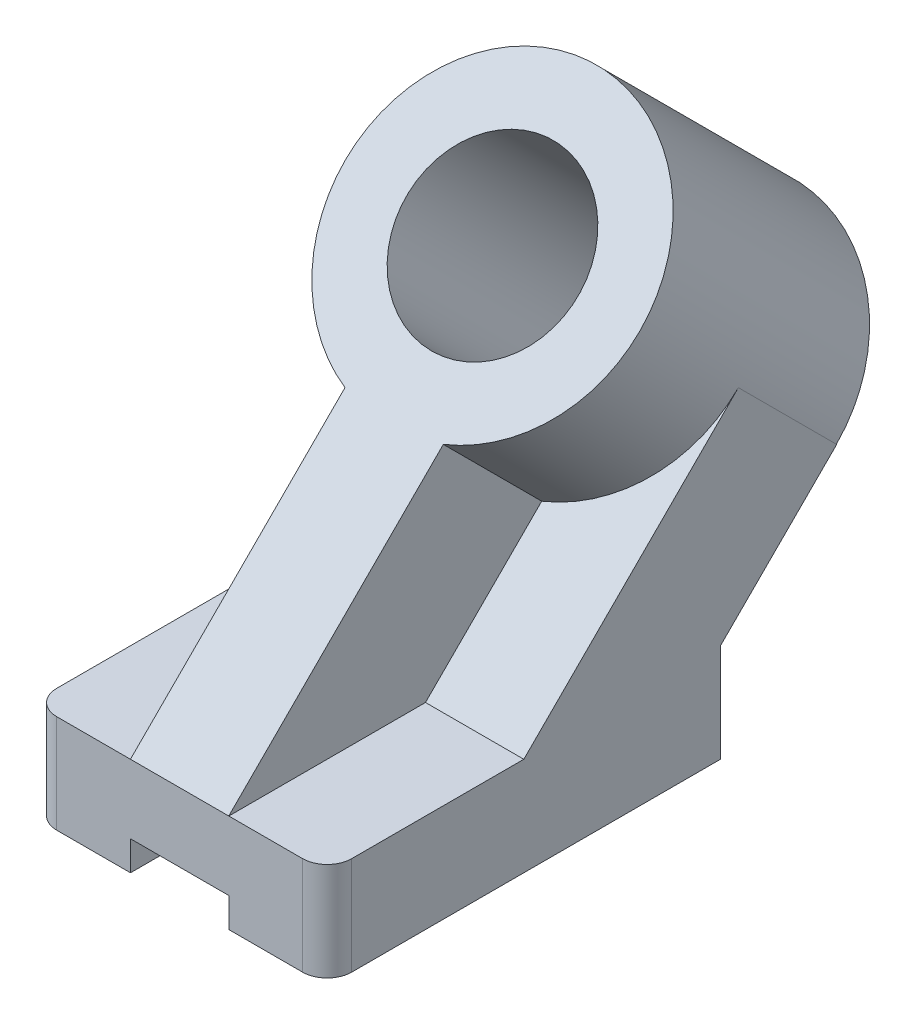
SolidWorks part; units mm, degrees
ref_plane "Front Plane" through (0, 0, 0) normal (0, 0, 1) x (1, 0, 0)
ref_plane "Top Plane" through (0, 0, 0) normal (0, 1, 0) x (1, 0, 0)
ref_plane "Right Plane" through (0, 0, 0) normal (1, 0, 0) x (0, 0, -1)
sketch "Sketch1" plane through (0, 0, 0) normal (0, 0, 1) x (1, 0, 0)
  line L1 (-47.0083, 1.6903) -> (29.1917, 1.6903)
  line L2 (-47.0083, 1.6903) -> (-47.0083, -23.7097)
  line L3 (-47.0083, -23.7097) -> (29.1917, -23.7097)
  line L4 (29.1917, 1.6903) -> (29.1917, -23.7097)
  dimension "D1" = 76.2
  dimension "D2" = 25.4
extrude "Boss-Extrude1" add sketch "Sketch1" against normal blind 101.6
sketch "Sketch3" plane through (29.1917, 0, 0) normal (1, 0, 0) x (0, 0, -1)
  line L0 (50.8, 1.6903) -> (50.8, -23.7097) construction
  line L1 (101.6, 1.6903) -> (0, 1.6903) construction
  line L2 (101.6, -23.7097) -> (0, -23.7097) construction
  line L3 (0, 1.6903) -> (80.8223, 82.5126) construction
  line L4 (80.8223, 82.5126) -> (134.619, 28.7159) construction
  line L5 (50.8, 1.6903) -> (106.2223, 57.1126)
  line L6 (101.6, 1.6903) -> (131.6223, 31.7126)
  line L7 (131.6223, 31.7126) -> (106.2223, 57.1126)
  line L8 (101.6, 1.6903) -> (50.8, 1.6903)
  dimension "D1" = 50.8
  dimension "D2" = 114.3
extrude "Boss-Extrude2" add sketch "Sketch3" against normal through all
sketch "Sketch4" plane through (0, -24.5549, -24.5549) normal (0, 0.7071, 0.7071) x (1, 0, 0)
  line L0 (-8.9083, 1.1952) -> (-8.9083, 115.4952) construction
  line L1 (29.1917, 1.1952) -> (-47.0083, 1.1952) construction
  line L2 (-47.0083, 115.4952) -> (29.1917, 115.4952) construction
  line L3 (-21.6083, 115.4952) -> (-47.0083, 115.4952) construction
  line L4 (-47.0083, 1.1952) -> (-21.6083, 1.1952) construction
  line L5 (29.1917, 1.1952) -> (3.7917, 1.1952) construction
  line L7 (-21.6083, 1.1952) -> (3.7917, 1.1952)
  line L8 (-21.6083, 1.1952) -> (-21.6083, 79.5742)
  line L10 (3.7917, 1.1952) -> (3.7917, 79.5742)
  arc A0 (3.7917, 79.5742) -> (-21.6083, 79.5742) centre (-8.9083, 115.4952) ccw
  dimension "D4" = 38.1
  dimension "D1" = 25.4
  dimension "D2" = 25.4
  dimension "D3" = 25.4
  dimension "D5" = 114.3
extrude "Boss-Extrude3" add sketch "Sketch4" along normal blind 35.941 and the other way blind 35.814
sketch "Sketch5" plane through (0, 0.8593, 0.8593) normal (0, 0.7071, 0.7071) x (1, 0, 0)
  line L0 (-8.9083, 153.5952) -> (-8.9083, 1.1952) construction
  line L1 (3.7917, 1.1952) -> (-21.6083, 1.1952) construction
  line L2 (-47.0083, 115.4952) -> (29.1917, 115.4952) construction
  arc A0 (3.7917, 79.5742) -> (-21.6083, 79.5742) centre (-8.9083, 115.4952) ccw construction
  circle A1 centre (-8.9083, 115.4952) radius 22.225
  dimension "D1" = 44.45
extrude "Cut-Extrude1" cut sketch "Sketch5" against normal through all
sketch "Sketch6" plane through (0, 1.6903, 0) normal (0, 1, 0) x (1, 0, 0)
  line L0 (-40.6583, 0) -> (-40.6583, 50.8) construction
  line L1 (-21.6083, 0) -> (-47.0083, 0) construction
  line L2 (-47.0083, 50.8) -> (-21.6083, 50.8) construction
  line L3 (-47.0083, 6.35) -> (29.1917, 6.35) construction
  line L4 (-47.0083, 50.8) -> (-47.0083, 0) construction
  line L5 (29.1917, 50.8) -> (29.1917, 0) construction
  line L6 (22.8417, 0) -> (22.8417, 50.8) construction
  line L7 (29.1917, 0) -> (3.7917, 0) construction
  line L8 (3.7917, 50.8) -> (29.1917, 50.8) construction
  line L9 (-47.0083, 6.35) -> (-47.0083, 0)
  line L10 (-47.0083, 0) -> (-40.6583, 0)
  line L11 (22.8417, 0) -> (29.1917, 0)
  line L12 (29.1917, 0) -> (29.1917, 6.35)
  arc A0 (-47.0083, 6.35) -> (-40.6583, 0) centre (-40.6583, 6.35) ccw
  arc A1 (29.1917, 6.35) -> (22.8417, 0) centre (22.8417, 6.35) cw
  dimension "D1" = 6.35
  dimension "D2" = 6.35
  dimension "D3" = 6.35
extrude "Cut-Extrude2" cut sketch "Sketch6" against normal through all
sketch "Sketch7" plane through (0, 0, 0) normal (0, 0, 1) x (1, 0, 0)
  line L2 (-21.6083, -23.7097) -> (-21.6083, -16.0897)
  line L3 (-21.6083, -16.0897) -> (3.7917, -16.0897)
  line L4 (3.7917, -23.7097) -> (3.7917, -16.0897)
  line L6 (-21.6083, -23.7097) -> (-21.6083, -49.034)
  line L7 (-21.6083, -49.034) -> (3.7917, -49.034)
  line L8 (3.7917, -23.7097) -> (3.7917, -49.034)
  point P6 (3.7917, -19.8997)
  point P7 (-21.6083, -19.8997)
  dimension "D1" = 7.62
  dimension "D2" = 25.4
  dimension "D3" = 25.4
extrude "Cut-Extrude3" cut sketch "Sketch7" against normal through all
